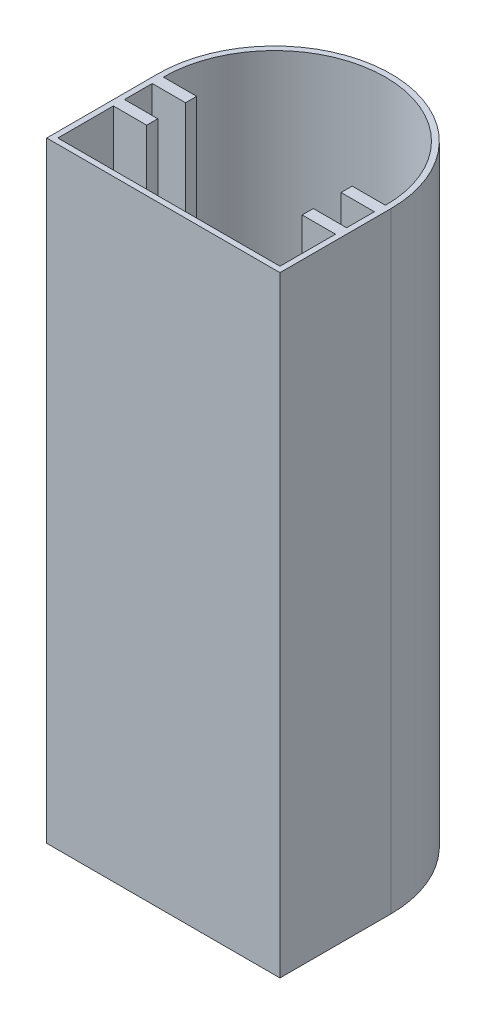
SolidWorks part; units mm, degrees
ref_plane "Front Plane" through (0, 0, 0) normal (0, 0, 1) x (1, 0, 0)
ref_plane "Top Plane" through (0, 0, 0) normal (0, 1, 0) x (1, 0, 0)
ref_plane "Right Plane" through (0, 0, 0) normal (1, 0, 0) x (0, 0, -1)
sketch "Sketch1" plane through (0, 0, 0) normal (0, 1, 0) x (1, 0, 0)
  line L0 (-40.8831, -1.7077) -> (1.1169, -1.7077)
  line L2 (-40.8831, -1.7077) -> (-40.8831, 18.2923)
  line L4 (1.1169, -1.7077) -> (1.1169, 18.2923)
  arc A0 (1.1169, 18.2923) -> (-40.8831, 18.2923) centre (-19.8831, 18.2923) ccw
  dimension "D3" = 21
  dimension "D1" = 42
  dimension "D2" = 20
extrude "Boss-Extrude1" add sketch "Sketch1" along normal blind 110 contours L2 A0 L4 L0
sketch "Sketch2" plane through (0, 110, 0) normal (0, 1, 0) x (1, 0, 0)
  line L5 (-39.8831, 16.2923) -> (-39.8831, 11.2923)
  line L6 (-39.8831, -0.7077) -> (0.1169, -0.7077)
  line L8 (-39.8831, 18.2923) -> (-33.8831, 18.2923)
  line L9 (-33.8831, 18.2923) -> (-33.8831, 16.2923)
  line L10 (-33.8831, 16.2923) -> (-39.8831, 16.2923)
  line L12 (-39.8831, 11.2923) -> (-33.8831, 11.2923)
  line L13 (-33.8831, 11.2923) -> (-33.8831, 9.2923)
  line L14 (-33.8831, 9.2923) -> (-39.8831, 9.2923)
  line L15 (0.1169, 9.2923) -> (0.1169, -0.7077)
  line L16 (-39.8831, 9.2923) -> (-39.8831, -0.7077)
  line L17 (-5.8831, 9.2923) -> (0.1169, 9.2923)
  line L18 (-5.8831, 11.2923) -> (-5.8831, 9.2923)
  line L19 (0.1169, 11.2923) -> (-5.8831, 11.2923)
  line L20 (-5.8831, 16.2923) -> (0.1169, 16.2923)
  line L21 (-5.8831, 18.2923) -> (-5.8831, 16.2923)
  line L22 (0.1169, 18.2923) -> (-5.8831, 18.2923)
  line L23 (-40.8831, -1.7077) -> (1.1169, -1.7077) construction
  line L24 (-40.8831, -1.7077) -> (-40.8831, 18.2923) construction
  line L25 (0.1169, 16.2923) -> (0.1169, 11.2923)
  arc A4 (0.1169, 18.2923) -> (-39.8831, 18.2923) centre (-19.8831, 18.2923) ccw
  point P7 (0, 0)
  point P8 (0, 0)
  point P25 (-19.8831, -0.7077)
  point P26 (0, 0)
  dimension "D13" = 20
  dimension "D1" = 6
  dimension "D2" = 2
  dimension "D3" = 5
  dimension "D4" = 2
  dimension "D5" = 6
  dimension "D6" = 1
  dimension "D7" = 1
  dimension "D8" = 6
  dimension "D9" = 5
  dimension "D10" = 2
  dimension "D11" = 2
  dimension "D12" = 1
  dimension "D14" = 6
extrude "Cut-Extrude1" cut sketch "Sketch2" against normal blind 109
sketch "Sketch3" plane through (-40.8831, 0, 0) normal (-1, 0, 0) x (0, 0, 1)
  line L0 (1.7077, 110) -> (1.7077, 0) construction
  line L1 (1.7077, 110) -> (-18.2923, 110) construction
  circle A0 centre (-4.9589, 55) radius 3.375
  point P4 (0, 0)
  dimension "D1" = 6.75
  dimension "D2" = 6.6667
  dimension "D3" = 55
extrude "Cut-Extrude2" cut sketch "Sketch3" against normal blind 5
equation "\"Width\" = 42"
equation "\"Depth\"= 20"
equation "\"lenght\"= 110"
equation "\"thick\"= 1"
equation "\"D1@Sketch1\"=\"Width\""
equation "\"D3@Sketch1\"=\"Width\"/2"
equation "\"length\"= 110"
equation "\"D1@Boss-Extrude1\"=\"length\""
equation "\"holder lenght\" = 6"
equation "\"holder width\"= 2"
equation "\"holder gap\" = 5"
equation "\"D1@Sketch2\"=\"holder lenght\""
equation "\"D2@Sketch2\"=\"holder width\""
equation "\"D3@Sketch2\"=\"holder gap\""
equation "\"D4@Sketch2\"=\"holder width\""
equation "\"D5@Sketch2\"=\"holder lenght\""
equation "\"D6@Sketch2\"=\"thick\""
equation "\"D7@Sketch2\"=\"thick\""
equation "\"D1@Cut-Extrude1\"=\"length\"-\"thick\""
equation "\"fillet\"= 0.5"
equation "\"D2@Sketch1\"=\"Depth\""
equation "\"D8@Sketch2\"=\"holder lenght\""
equation "\"D9@Sketch2\"=\"holder gap\""
equation "\"D10@Sketch2\"=\"holder width\""
equation "\"D11@Sketch2\"=\"holder width\""
equation "\"hole\"= 6.75"
equation "\"D1@Sketch3\"=\"hole\""
equation "\"D2@Sketch3\"=\"Depth\"/3"
equation "\"D3@Sketch3\"=\"lenght\"/2"
equation "\"D12@Sketch2\"=\"thick\""
equation "\"D13@Sketch2\"=\"Width\"/2-\"thick\""
equation "\"D14@Sketch2\"=\"holder lenght\""
